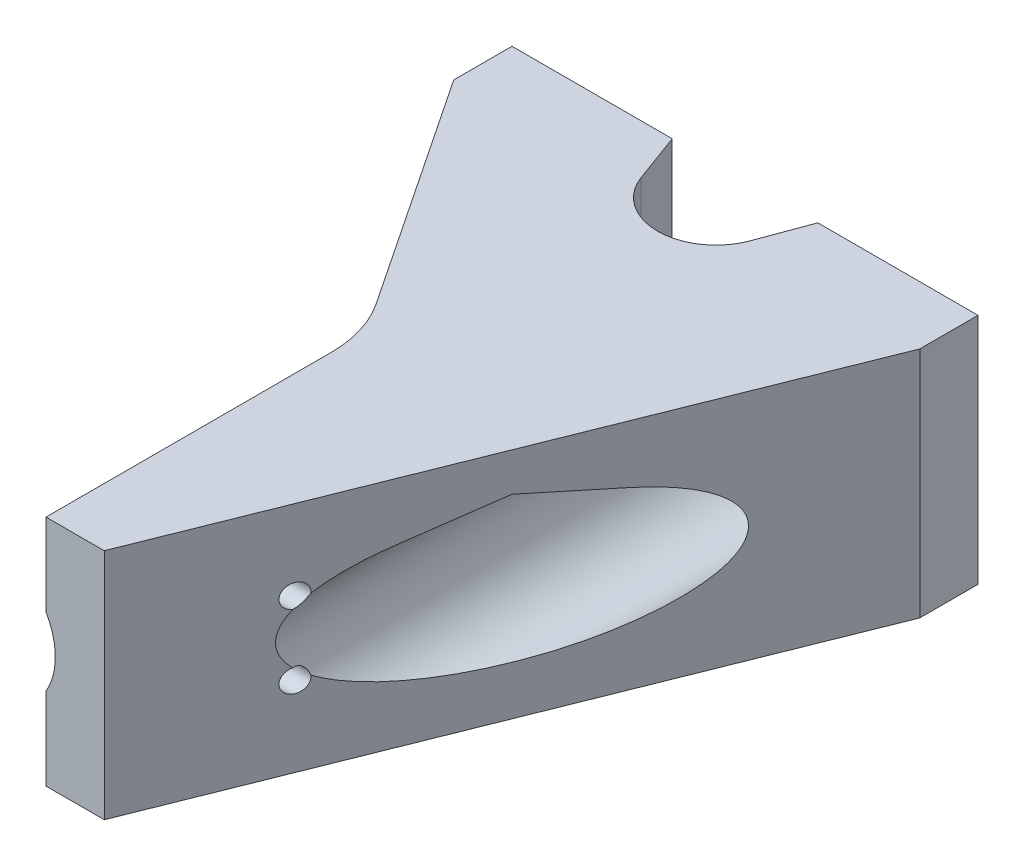
SolidWorks part; units mm, degrees
material "PET"
ref_plane "Front" through (0, 0, 0) normal (0, 0, 1) x (1, 0, 0)
ref_plane "Top" through (0, 0, 0) normal (0, 1, 0) x (1, 0, 0)
ref_plane "Right" through (0, 0, 0) normal (1, 0, 0) x (0, 0, -1)
sketch "Sketch1" plane through (0, 0, 0) normal (0, 1, 0) x (1, 0, 0)
  line L0 (0, 0) -> (17.4625, 0)
  line L1 (50.8, 0) -> (50.8, -6.35)
  line L3 (50.8, -6.35) -> (25.4, -69.85)
  line L4 (25.4, -69.85) -> (19.05, -69.85)
  line L5 (0, -6.35) -> (0, 0)
  line L6 (17.4625, 0) -> (19.4417, -5.3707)
  line L7 (31.3583, -5.3707) -> (33.3375, 0)
  line L8 (33.3375, 0) -> (50.8, 0)
  line L9 (19.05, -69.85) -> (19.05, -38.7703)
  line L10 (16.917, -31.7256) -> (0, -6.35)
  arc A0 (19.4417, -5.3707) -> (31.3583, -5.3707) centre (25.4, -3.175) ccw
  arc A1 (19.05, -38.7703) -> (16.917, -31.7256) centre (6.35, -38.7703) ccw
  point P20 (19.05, -34.925)
  dimension "D6" = 6.35
  dimension "D7" = 9.525
  dimension "D10" = 12.7
  dimension "D1" = 50.8
  dimension "D2" = 6.35
  dimension "D3" = 69.85
  dimension "D4" = 31.75
  dimension "D5" = 34.925
  dimension "D8" = 15.875
  dimension "D9" = 6.35
extrude "Boss-Extrude1" add sketch "Sketch1" along normal mid plane 25.4
sketch "Sketch2" plane through (0, 0, 0) normal (0, 1, 0) x (1, 0, 0)
  line L0 (12.7, 0) -> (12.7, -120.015)
  line L1 (17.4625, 0) -> (0, 0) construction
  line L2 (12.7, -120.015) -> (5.334, -120.015)
  line L3 (5.334, -120.015) -> (5.334, -9.525)
  line L4 (5.334, -9.525) -> (10.1473, -9.525)
  line L5 (10.1473, -9.525) -> (10.1473, 0)
  line L6 (10.1473, 0) -> (12.7, 0)
  line L7 (12.7, 0) -> (12.7, 3.0151) construction
  line L8 (25.4, -3.175) -> (25.4, 4.4959) construction
  line L9 (25.4, -69.85) -> (50.8, -6.35) construction
  dimension "D1" = 5.1054
  dimension "D2" = 9.525
  dimension "D3" = 14.732
  dimension "D4" = 25.4
revolve "Cut-Revolve1" cut sketch "Sketch2" angle 360 about L7
sketch "Sketch6" plane through (0, 0, 9.525) normal (0, 0, 1) x (1, 0, 0)
  line L0 (11.4236, 2.2107) -> (12.7, 2.9476)
  line L1 (12.7, 2.9476) -> (13.9764, 2.2107)
  circle A0 centre (12.7, 0) radius 2.5527 construction
  arc A1 (13.9764, 2.2107) -> (11.4236, 2.2107) centre (12.7, 0) ccw
  point P4 (0, 0)
  dimension "D1" = 30
extrude "Cut-Extrude1" cut sketch "Sketch6" against normal through all
sketch "Sketch7" plane through (0, 0, 9.525) normal (0, 0, 1) x (1, 0, 0)
  line L0 (9.017, 6.3791) -> (12.7, 8.5055)
  line L1 (12.7, 8.5055) -> (16.383, 6.3791)
  circle A0 centre (12.7, 0) radius 7.366 construction
  arc A1 (16.383, 6.3791) -> (9.017, 6.3791) centre (12.7, 0) ccw
  point P4 (17.5131, 5.576)
  point P6 (0, 0)
  dimension "D1" = 30
extrude "Cut-Extrude2" cut sketch "Sketch7" along normal through all
pattern_linear "LPattern1" count 2 spacing 25.4 along (1, 0, 0) of "Cut-Revolve1", "Cut-Extrude1", "Cut-Extrude2"
sketch "Sketch5" plane through (19.05, 0, 0) normal (-1, 0, 0) x (0, 0, 1)
  line L0 (55, 4) -> (55, 12.7) construction
  line L1 (38.7703, 12.7) -> (69.85, 12.7) construction
  line L6 (55, -4) -> (55, -12.7) construction
  line L7 (38.7703, -12.7) -> (69.85, -12.7) construction
  line L9 (0, 12.7) -> (0, -12.7) construction
  point P0 (55, 4)
  point P2 (55, -4)
  dimension "D1" = 55
  dimension "D2" = 8
hole_wizard "M3x0.5 Tapped Hole1" positions "Sketch5" profile "Sketch4" tap size "M3x0.5" standard "ANSI Metric" end condition through all
sketch "Sketch4" plane through (19.05, 4, 55) normal (0, 1, 0) x (0, 0, 1)
  line L0 (0, 0) -> (0, 31.75)
  line L1 (0, 31.75) -> (1.25, 31.75)
  line L2 (1.25, 31.75) -> (1.25, 0)
  line L5 (1.25, 0) -> (0, 0)
  line L11 (0, -6.35) -> (0, 107.95) construction
  dimension "Thru Tap Drill Dia." = 2.5
  dimension "Thru Tap Drill Depth" = 31.75
cosmetic thread "Hole Thread1" parameters "D2"=3
cosmetic thread "Hole Thread2" parameters "D2"=3
